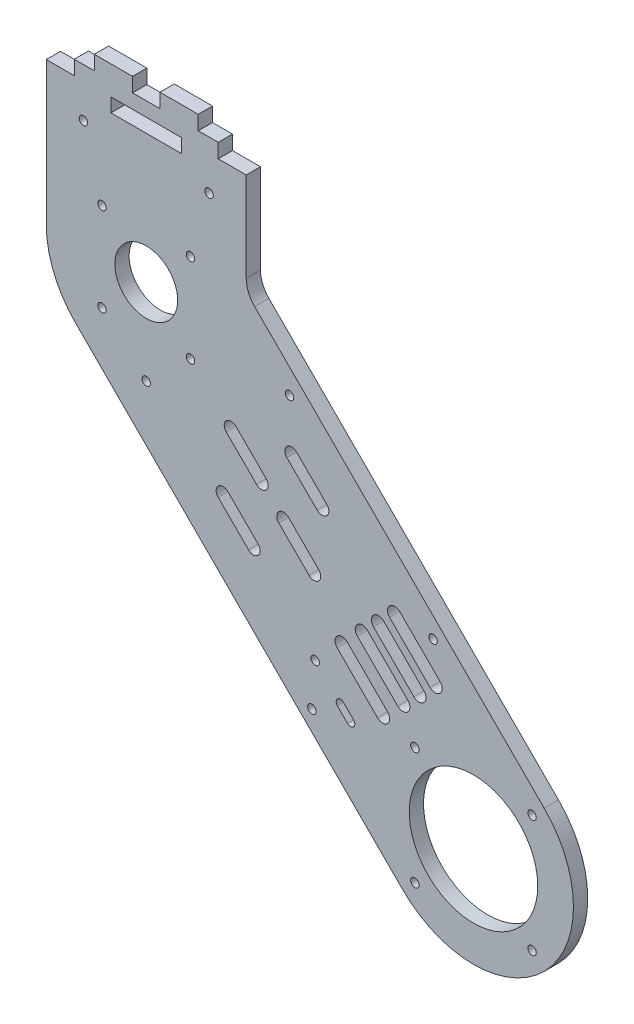
SolidWorks part; units mm, degrees
ref_plane "Front Plane" through (0, 0, 0) normal (0, 0, 1) x (1, 0, 0)
ref_plane "Top Plane" through (0, 0, 0) normal (0, 1, 0) x (1, 0, 0)
ref_plane "Right Plane" through (0, 0, 0) normal (1, 0, 0) x (0, 0, -1)
sketch "Sketch1" plane through (0, 0, 0) normal (0, 0, 1) x (1, 0, 0)
  line L0 (0, 0) -> (35, 0) construction
  line L1 (0, 0) -> (0, 35) construction
  line L2 (0, 0) -> (24.7487, 24.7487) construction
  line L3 (0, 0) -> (-24.7487, -24.7487) construction
  line L4 (-24.7487, -24.7487) -> (-139.3, 89.8026)
  line L5 (0, 0) -> (24.7487, -24.7487) construction
  line L6 (-139.3, 89.8026) -> (-114.5513, 114.5513) construction
  line L7 (24.7487, 24.7487) -> (-54.6728, 104.1703)
  line L8 (-33.234, 51.6188) -> (-19.0919, 37.4767) construction
  line L9 (-31.4663, 53.3866) -> (-17.3241, 39.2444)
  line L10 (-35.0018, 49.851) -> (-20.8597, 35.7089)
  line L11 (-114.5513, 114.5513) -> (0, 0) construction
  line L12 (-38.8909, 45.9619) -> (-24.7487, 31.8198) construction
  line L13 (-37.1231, 47.7297) -> (-22.981, 33.5876)
  line L14 (-40.6586, 44.1942) -> (-26.5165, 30.052)
  line L15 (-31.8198, 38.8909) -> (-10.6066, 60.1041) construction
  line L16 (-27.5772, 57.2756) -> (-13.435, 43.1335) construction
  line L17 (-25.8094, 59.0434) -> (-11.6673, 44.9013)
  line L18 (-29.3449, 55.5079) -> (-15.2028, 41.3657)
  line L19 (-31.8198, 38.8909) -> (-60.1041, 10.6066) construction
  line L20 (-45.9619, 38.8909) -> (-31.8198, 24.7487) construction
  line L21 (-44.1942, 40.6586) -> (-30.052, 26.5165)
  line L22 (-47.7297, 37.1231) -> (-33.5876, 22.981)
  line L23 (-84.8528, 84.8528) -> (-74.2462, 74.2462) construction
  line L24 (-83.1558, 86.5499) -> (-72.5492, 75.9433)
  line L25 (-86.5499, 83.1558) -> (-75.9433, 72.5492)
  line L26 (-64.3969, 105.3087) -> (-109.6016, 60.1041) construction
  line L27 (-66.468, 66.468) -> (-55.8614, 55.8614) construction
  line L28 (-64.771, 68.1651) -> (-54.1644, 57.5585)
  line L29 (-68.1651, 64.771) -> (-57.5585, 54.1644)
  line L30 (-63.6396, 87.6812) -> (-53.033, 77.0746) construction
  line L33 (-74.2462, 74.2462) -> (-49.4975, 98.9949) construction
  line L34 (-70.3571, 70.3571) -> (-45.6084, 95.1059) construction
  line L35 (-61.9426, 89.3783) -> (-51.336, 78.7717)
  line L36 (-65.3367, 85.9842) -> (-54.7301, 75.3776)
  line L37 (-87.6812, 63.6396) -> (-77.0746, 53.033) construction
  line L38 (-89.3783, 61.9426) -> (-78.7717, 51.336)
  line L39 (-85.9842, 65.3367) -> (-75.3776, 54.7301)
  line L40 (-114.5513, 114.5513) -> (-207.3962, 114.5513) construction
  line L41 (-149.5513, 114.5513) -> (-149.5513, 164.5513)
  line L42 (-114.5513, 114.5513) -> (-8.6743, 114.5513) construction
  line L43 (-79.5513, 133.1909) -> (-79.5513, 165.6653)
  line L44 (-114.5513, 114.5513) -> (-79.5513, 149.5513) construction
  line L45 (-54.6728, 104.1703) -> (-76.6224, 126.1198)
  line L46 (-114.5513, 114.5513) -> (-146.8871, 101.1574) construction
  line L47 (-146.8871, 101.1574) -> (-49.8797, 141.3391) construction
  line L48 (-114.5513, 114.5513) -> (-114.5513, 83.0763) construction
  line L49 (-132.7513, 174.5513) -> (-119.3513, 174.5513) construction
  line L50 (-79.5513, 165.6653) -> (-79.5513, 174.5513)
  line L51 (-119.3513, 169.5513) -> (-109.7513, 169.5513)
  line L52 (-114.5513, 114.5513) -> (-114.5513, 174.5513) construction
  line L53 (-119.3513, 174.5513) -> (-132.7513, 174.5513)
  line L54 (-126.9013, 164.5513) -> (-102.2013, 164.5513)
  line L55 (-126.9013, 164.5513) -> (-126.9013, 159.7013)
  line L56 (-126.9013, 159.7013) -> (-102.2013, 159.7013)
  line L57 (-102.2013, 164.5513) -> (-102.2013, 159.7013)
  line L58 (-139.7513, 169.5513) -> (-132.7513, 169.5513) construction
  line L59 (-46.563, 20.6122) -> (-43.0274, 17.0766) construction
  line L60 (-132.7513, 174.5513) -> (-132.7513, 169.5513) construction
  line L61 (-119.3513, 169.5513) -> (-119.3513, 174.5513)
  line L62 (-114.5513, 174.5513) -> (-96.3513, 174.5513) construction
  line L63 (-114.5513, 159.7013) -> (-114.5513, 164.5513) construction
  line L64 (-126.9013, 162.1263) -> (-102.2013, 162.1263) construction
  line L65 (-149.5513, 164.5513) -> (-79.5513, 164.5513) construction
  line L66 (-132.7513, 169.5513) -> (-139.7513, 169.5513)
  line L67 (-139.7513, 169.5513) -> (-139.7513, 164.5513)
  line L68 (-139.7513, 164.5513) -> (-149.5513, 164.5513)
  line L69 (-132.7513, 169.5513) -> (-132.7513, 174.5513)
  line L70 (-109.7513, 169.5513) -> (-109.7513, 174.5513)
  line L71 (-109.7513, 174.5513) -> (-96.3513, 174.5513)
  line L72 (-96.3513, 169.5513) -> (-96.3513, 174.5513)
  line L73 (-96.3513, 169.5513) -> (-89.3513, 169.5513)
  line L74 (-89.3513, 169.5513) -> (-89.3513, 164.5513)
  line L75 (-89.3513, 164.5513) -> (-79.5513, 164.5513)
  line L76 (-119.3513, 169.5513) -> (-109.7513, 169.5513) construction
  line L77 (-96.3513, 169.5513) -> (-89.3513, 169.5513) construction
  line L78 (-45.5023, 21.6728) -> (-41.9668, 18.1373)
  line L79 (-47.6236, 19.5515) -> (-44.0881, 16.016)
  circle A0 centre (0, 0) radius 22.5
  arc A1 (-24.7487, -24.7487) -> (24.7487, 24.7487) centre (0, 0) ccw
  circle A2 centre (-114.5513, 114.5513) radius 11
  circle A3 centre (20.5061, -20.5061) radius 1.475
  circle A4 centre (-20.5061, -20.5061) radius 1.475
  circle A5 centre (-20.5061, 20.5061) radius 1.475
  circle A6 centre (20.5061, 20.5061) radius 1.475
  arc A7 (-31.4663, 53.3866) -> (-35.0018, 49.851) centre (-33.234, 51.6188) ccw
  arc A8 (-20.8597, 35.7089) -> (-17.3241, 39.2444) centre (-19.0919, 37.4767) ccw
  arc A9 (-37.1231, 47.7297) -> (-40.6586, 44.1942) centre (-38.8909, 45.9619) ccw
  arc A10 (-26.5165, 30.052) -> (-22.981, 33.5876) centre (-24.7487, 31.8198) ccw
  arc A11 (-25.8094, 59.0434) -> (-29.3449, 55.5079) centre (-27.5772, 57.2756) ccw
  arc A12 (-15.2028, 41.3657) -> (-11.6673, 44.9013) centre (-13.435, 43.1335) ccw
  arc A13 (-44.1942, 40.6586) -> (-47.7297, 37.1231) centre (-45.9619, 38.8909) ccw
  arc A14 (-33.5876, 22.981) -> (-30.052, 26.5165) centre (-31.8198, 24.7487) ccw
  circle A15 centre (-14.1421, 56.5685) radius 1.475
  circle A16 centre (-56.5685, 14.1421) radius 1.475
  circle A17 centre (-64.3969, 105.3087) radius 1.475
  arc A18 (-83.1558, 86.5499) -> (-86.5499, 83.1558) centre (-84.8528, 84.8528) ccw
  arc A19 (-75.9433, 72.5492) -> (-72.5492, 75.9433) centre (-74.2462, 74.2462) ccw
  arc A20 (-64.771, 68.1651) -> (-68.1651, 64.771) centre (-66.468, 66.468) ccw
  arc A21 (-57.5585, 54.1644) -> (-54.1644, 57.5585) centre (-55.8614, 55.8614) ccw
  arc A24 (-61.9426, 89.3783) -> (-65.3367, 85.9842) centre (-63.6396, 87.6812) ccw
  arc A25 (-54.7301, 75.3776) -> (-51.336, 78.7717) centre (-53.033, 77.0746) ccw
  arc A26 (-89.3783, 61.9426) -> (-85.9842, 65.3367) centre (-87.6812, 63.6396) cw
  arc A27 (-75.3776, 54.7301) -> (-78.7717, 51.336) centre (-77.0746, 53.033) cw
  arc A29 (-149.5513, 114.5513) -> (-139.3, 89.8026) centre (-114.5513, 114.5513) ccw
  arc A31 (-76.6224, 126.1198) -> (-79.5513, 133.1909) centre (-69.5513, 133.1909) cw
  circle A32 centre (-99.0513, 130.0513) radius 1.475
  circle A33 centre (-99.0513, 99.0513) radius 1.475
  circle A34 centre (-130.0513, 99.0513) radius 1.475
  circle A35 centre (-130.0513, 130.0513) radius 1.475
  circle A36 centre (-114.5513, 84.5513) radius 1.475
  circle A37 centre (-136.5513, 152.5513) radius 1.475
  circle A38 centre (-92.5513, 152.5513) radius 1.475
  circle A39 centre (-55.4018, 29.451) radius 1.475
  arc A40 (-45.5023, 21.6728) -> (-47.6236, 19.5515) centre (-46.563, 20.6122) ccw
  arc A41 (-44.0881, 16.016) -> (-41.9668, 18.1373) centre (-43.0274, 17.0766) ccw
  point P23 (0, 0)
  point P24 (-26.163, 44.5477)
  point P31 (-31.8198, 38.8909)
  point P42 (-20.5061, 50.2046)
  point P47 (-38.8909, 31.8198)
  point P59 (-79.5495, 79.5495)
  point P68 (-61.1647, 61.1647)
  point P76 (-58.3363, 82.3779)
  point P92 (-82.3779, 58.3363)
  point P107 (-79.5513, 129.0488)
  point P116 (-114.5513, 114.5513)
  point P123 (-114.5513, 162.1263)
  point P144 (-44.7952, 18.8444)
  dimension "D1" = 45
  dimension "D2" = 70
  dimension "D6" = 22
  dimension "D7" = 2.95
  dimension "D12" = 2.5
  dimension "D15" = 2.5
  dimension "D20" = 2.95
  dimension "D22" = 2.95
  dimension "D25" = 2.4
  dimension "D29" = 2.4
  dimension "D30" = 17
  dimension "D31" = 5.5
  dimension "D35" = 35.1835
  dimension "D36" = 32.1163
  dimension "D37" = 10
  dimension "D38" = 2.95
  dimension "D41" = 2.95
  dimension "D43" = 2.95
  dimension "D46" = 2.95
  dimension "D58" = 1.5
  dimension "D3" = 45
  dimension "D4" = 180
  dimension "D5" = 162
  dimension "D8" = 29
  dimension "D10" = 35
  dimension "D11" = 20
  dimension "D13" = 5
  dimension "D14" = 20
  dimension "D16" = 50
  dimension "D17" = 8
  dimension "D18" = 8
  dimension "D19" = 10
  dimension "D21" = 5
  dimension "D23" = 6.071
  dimension "D24" = 70
  dimension "D26" = 15
  dimension "D27" = 11
  dimension "D28" = 15
  dimension "D32" = 70
  dimension "D33" = 35
  dimension "D34" = 180
  dimension "D39" = 15.5
  dimension "D42" = 30
  dimension "D44" = 13
  dimension "D45" = 38
  dimension "D47" = 18.2
  dimension "D48" = 12.425
  dimension "D49" = 10
  dimension "D50" = 24.7
  dimension "D51" = 5
  dimension "D52" = 13.4
  dimension "D53" = 5
  dimension "D54" = 25.2
  dimension "D55" = 60
  dimension "D56" = 16.65
  dimension "D57" = 16.65
  dimension "D59" = 5
  dimension "D60" = 12.5
  dimension "D9" = 4
  dimension "D40" = 4
extrude "Boss-Extrude1" add sketch "Sketch1" against normal blind 5 contours L45 A31 L43 L75 L74 L73 L72 L71 L70 L51 L61 L53 L69 L66 L67 L68 L41 A29 L4 A1 L7 A41 L79 A40 L78 A39 A25 L36 A24 L35 A21 L29 A20 L28 A19 L25 A18 L24 A17 L54 L57 L56 L55
